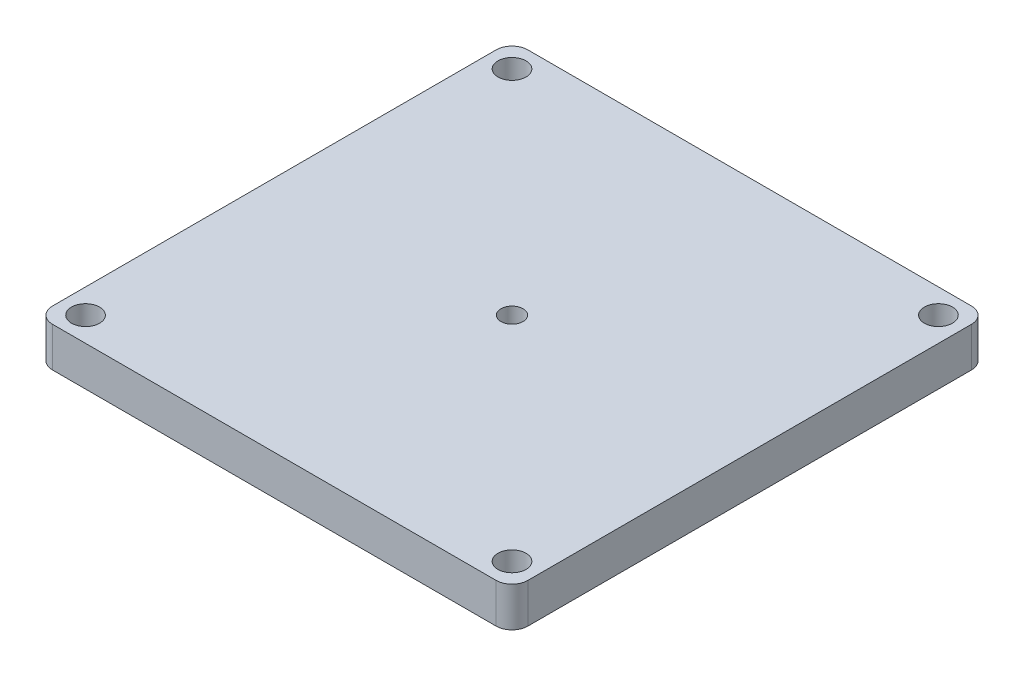
SolidWorks part; units mm, degrees
ref_plane "Front Plane" through (0, 0, 0) normal (0, 0, 1) x (1, 0, 0)
ref_plane "Top Plane" through (0, 0, 0) normal (0, 1, 0) x (1, 0, 0)
ref_plane "Right Plane" through (0, 0, 0) normal (1, 0, 0) x (0, 0, -1)
sketch "Sketch1" plane through (0, 0, 0) normal (0, 1, 0) x (1, 0, 0)
  line L1 (-38.1, -38.1) -> (38.1, -38.1)
  line L2 (-38.1, -38.1) -> (-38.1, 38.1)
  line L3 (-38.1, 38.1) -> (38.1, 38.1)
  line L4 (38.1, -38.1) -> (38.1, 38.1)
  line L5 (-38.1, -38.1) -> (38.1, 38.1) construction
  line L6 (-38.1, 38.1) -> (38.1, -38.1) construction
  point P0 (0, 0)
  dimension "D1" = 76.2
  dimension "D2" = 76.2
extrude "Boss-Extrude1" add sketch "Sketch1" along normal blind 6.35
fillet "Fillet1" radius 2.54 4 edges at (38.1, 3.175, 38.1) (-38.1, 3.175, 38.1) (-38.1, 3.175, -38.1) (38.1, 3.175, -38.1)
sketch "Sketch3" plane through (0, 6.35, 0) normal (0, 1, 0) x (1, 0, 0)
  circle A0 centre (0, 0) radius 1.78
  dimension "D1" = 3.56
extrude "Cut-Extrude1" cut sketch "Sketch3" against normal through all
sketch "Sketch4" plane through (0, 0, 0) normal (0, -1, 0) x (1, 0, 0)
  line L5 (31.75, -31.75) -> (-31.75, -31.75)
  line L6 (31.75, -31.75) -> (31.75, 31.75)
  line L7 (31.75, 31.75) -> (-31.75, 31.75)
  line L8 (-31.75, -31.75) -> (-31.75, 31.75)
  line L9 (31.75, -31.75) -> (-31.75, 31.75) construction
  line L10 (31.75, 31.75) -> (-31.75, -31.75) construction
  point P9 (0, 0)
extrude "Boss-Extrude2" add sketch "Sketch4" along normal blind 2.54
fillet "Fillet2" radius 2.54 4 edges at (-31.75, -1.27, 31.75) (31.75, -1.27, 31.75) (31.75, -1.27, -31.75) (-31.75, -1.27, -31.75)
sketch "Sketch5" plane through (0, -2.54, 0) normal (0, -1, 0) x (1, 0, 0)
  line L0 (-37.3561, 37.3561) -> (-31.0061, 31.0061) construction
  line L1 (31.0061, 31.0061) -> (37.3561, 37.3561) construction
  line L2 (31.0061, -31.0061) -> (37.3561, -37.3561) construction
  line L3 (-31.0061, -31.0061) -> (-37.3561, -37.3561) construction
  line L4 (-34.1811, 34.1811) -> (-34.1811, -34.1811) construction
  line L5 (-34.1811, -34.1811) -> (34.1811, -34.1811) construction
  line L6 (34.1811, -34.1811) -> (34.1811, 34.1811) construction
  line L7 (34.1811, 34.1811) -> (-34.1811, 34.1811) construction
  arc A0 (-35.56, 38.1) -> (-38.1, 35.56) centre (-35.56, 35.56) ccw construction
  arc A1 (-29.21, 31.75) -> (-31.75, 29.21) centre (-29.21, 29.21) ccw construction
  arc A2 (31.75, 29.21) -> (29.21, 31.75) centre (29.21, 29.21) ccw construction
  arc A3 (38.1, 35.56) -> (35.56, 38.1) centre (35.56, 35.56) ccw construction
  arc A4 (29.21, -31.75) -> (31.75, -29.21) centre (29.21, -29.21) ccw construction
  arc A5 (35.56, -38.1) -> (38.1, -35.56) centre (35.56, -35.56) ccw construction
  arc A6 (-31.75, -29.21) -> (-29.21, -31.75) centre (-29.21, -29.21) ccw construction
  arc A7 (-38.1, -35.56) -> (-35.56, -38.1) centre (-35.56, -35.56) ccw construction
  point P32 (-34.1811, 34.1811)
  point P33 (-34.1811, -34.1811)
  point P34 (34.1811, -34.1811)
  point P36 (34.1811, 34.1811)
  point P47 (-34.1811, -34.1811)
  point P49 (34.1811, -34.1811)
  point P51 (34.1811, 34.1811)
  point P53 (-34.1811, 34.1811)
hole_wizard "M4 Clearance Hole2" positions "Sketch5" profile "Sketch6" hole size "M4" standard "ANSI Metric"
sketch "Sketch6" plane through (-34.1811, -2.54, 34.1811) normal (1, 0, 0) x (0, 0, -1)
  line L0 (0, 0) -> (0, 15.3219)
  line L1 (0, 15.3219) -> (2.25, 13.97)
  line L2 (2.25, 13.97) -> (2.25, 0)
  line L5 (2.25, 0) -> (0, 0)
  line L10 (0, 15.3219) -> (-2.25, 13.97) construction
  line L11 (0, -6.35) -> (0, 107.95) construction
  dimension "Hole Dia." = 4.5
  dimension "Hole Depth" = 13.97
  dimension "Drill Angle" = 118
sketch "Sketch7" plane through (0, -2.54, 0) normal (0, -1, 0) x (-1, 0, 0)
  line L5 (25.4, 29.845) -> (-25.4, 29.845)
  line L6 (25.4, 29.845) -> (25.4, 26.035)
  line L7 (25.4, 26.035) -> (-25.4, 26.035)
  line L8 (-25.4, 29.845) -> (-25.4, 26.035)
  line L9 (25.4, 29.845) -> (-25.4, 26.035) construction
  line L10 (25.4, 26.035) -> (-25.4, 29.845) construction
  line L11 (25.4, -29.845) -> (-25.4, -29.845)
  line L12 (25.4, -29.845) -> (25.4, -26.035)
  line L13 (25.4, -26.035) -> (-25.4, -26.035)
  line L14 (-25.4, -29.845) -> (-25.4, -26.035)
  line L15 (25.4, -29.845) -> (-25.4, -26.035) construction
  line L16 (25.4, -26.035) -> (-25.4, -29.845) construction
  point P0 (0, 0)
  dimension "D3" = 50.8
  dimension "D4" = 3.81
  dimension "D5" = 50.8
  dimension "D6" = 3.81
extrude "Cut-Extrude2" cut sketch "Sketch7" against normal blind 5.08
fillet "Fillet3" radius 1.27 8 edges at (-25.4, 0, -26.035) (-25.4, 0, -29.845) (25.4, 0, -26.035) (25.4, 0, -29.845) (25.4, 0, 26.035) (25.4, 0, 29.845) (-25.4, 0, 26.035) (-25.4, 0, 29.845)
